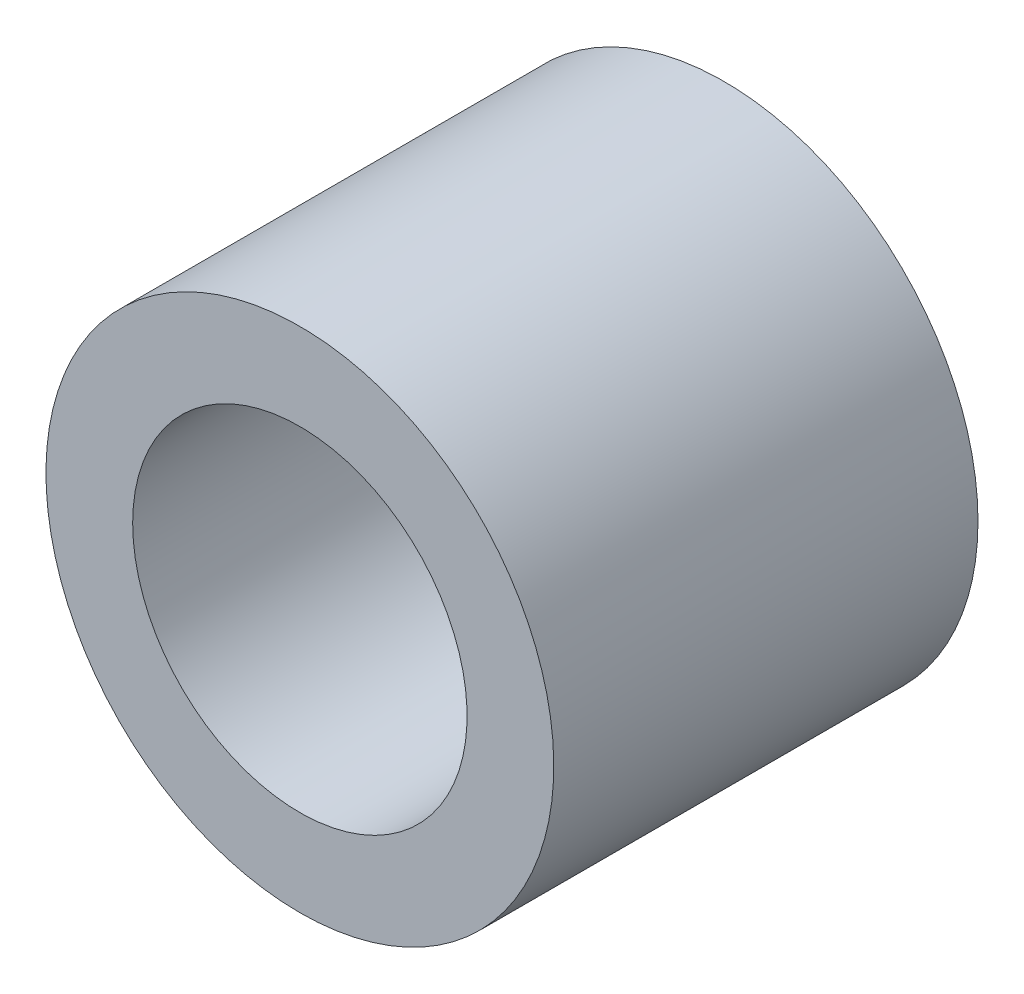
SolidWorks part; units mm, degrees
ref_plane "Front Plane" through (0, 0, 0) normal (0, 0, 1) x (1, 0, 0)
ref_plane "Top Plane" through (0, 0, 0) normal (0, 1, 0) x (1, 0, 0)
ref_plane "Right Plane" through (0, 0, 0) normal (1, 0, 0) x (0, 0, -1)
sketch "Sketch1" plane through (0, 0, 0) normal (0, 0, 1) x (1, 0, 0)
  circle A3 centre (59.4755, 35.57) radius 4.1
extrude "Boss-Extrude2" add sketch "Sketch1" along normal up to surface (6.85 mm away)
hole_wizard "M5 Clearance Hole1" positions "Sketch2" profile "Sketch3" hole size "M5" standard "ISO" end condition through all
sketch "Sketch2" plane through (0, 0, 0) normal (0, 0, -1) x (-1, 0, 0)
  point P0 (-59.4755, 35.57)
sketch "Sketch3" plane through (59.4755, 35.57, 0) normal (1, 0, 0) x (0, 1, 0)
  line L0 (0, 0) -> (0, 6.85)
  line L1 (0, 6.85) -> (2.7, 6.85)
  line L2 (2.7, 6.85) -> (2.7, 0)
  line L5 (2.7, 0) -> (0, 0)
  line L11 (0, -6.35) -> (0, 107.95) construction
  dimension "Thru Hole Dia." = 5.4
  dimension "Thru Hole Depth" = 6.85
